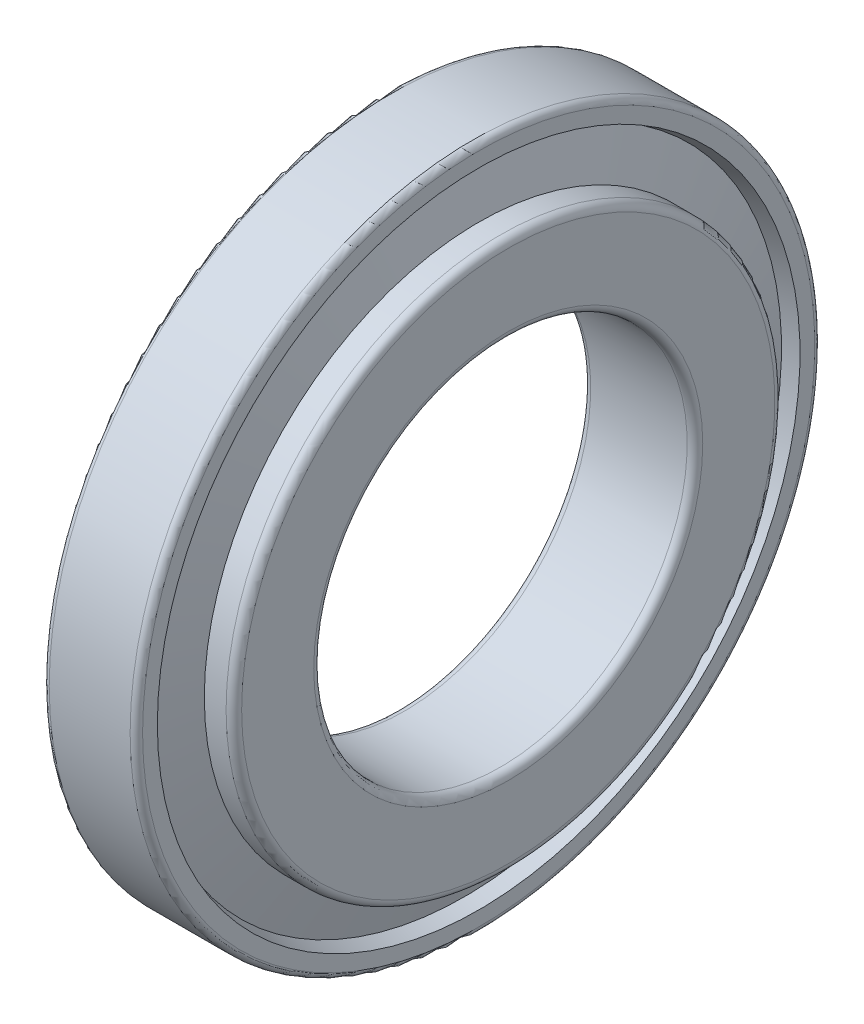
SolidWorks part; units mm, degrees
material "AISI Тип A2 Инструментальная сталь"
ref_plane "Спереди" through (0, 0, 0) normal (0, 0, 1) x (1, 0, 0)
ref_plane "Сверху" through (0, 0, 0) normal (0, 1, 0) x (1, 0, 0)
ref_plane "Справа" through (0, 0, 0) normal (1, 0, 0) x (0, 0, -1)
sketch "Эскиз1" plane through (0, 0, 0) normal (0, 0, 1) x (1, 0, 0)
  line L20 (-882.5277, 0) -> (43243.8573, 0) construction
  line L33 (15.3618, 192.3582) -> (0, 187.488)
  line L34 (0, 187.488) -> (0, 216)
  line L35 (4, 220) -> (56, 220)
  line L36 (60, 216) -> (60, 206.51)
  line L37 (60, 206.51) -> (50.9537, 203.642)
  line L38 (15.3618, 192.3582) -> (50.9537, 203.642) construction
  line L39 (23.7235, 162.4947) -> (7, 162.4947)
  line L40 (7, 162.4947) -> (7, 125)
  line L41 (12, 120) -> (74, 120)
  line L42 (79, 125) -> (79, 171.334)
  line L43 (74, 176.334) -> (60, 176.334)
  line L44 (60, 176.334) -> (60, 171.334)
  line L45 (23.7235, 162.4947) -> (60, 171.334) construction
  line L46 (60, 171.334) -> (50.9537, 203.642)
  line L47 (23.7235, 162.4947) -> (15.3618, 192.3582)
  line L48 (19.5427, 177.4264) -> (55.4769, 187.488) construction
  line L49 (0, 187.488) -> (55.4769, 187.488) construction
  line L50 (15.3618, 192.3582) -> (15.3618, 162.4947) construction
  arc A0 (0, 216) -> (4, 220) centre (4, 216) cw
  arc A1 (56, 220) -> (60, 216) centre (56, 216) cw
  arc A2 (7, 125) -> (12, 120) centre (12, 125) ccw
  arc A3 (79, 125) -> (74, 120) centre (74, 125) cw
  arc A4 (74, 176.334) -> (79, 171.334) centre (74, 171.334) cw
  point P12 (55.4769, 187.488)
  dimension "гост r1" = 5
  dimension "гост r2" = 4
  dimension "гост DD" = 440
  dimension "гост B" = 72
  dimension "гост C" = 60
  dimension "гост T" = 79
  dimension "гост E" = 374.976
  dimension "гост d" = 240
  dimension "гост alfa" = 15.642
revolve "Повернуть1" add sketch "Эскиз1" angle 360 about L20
